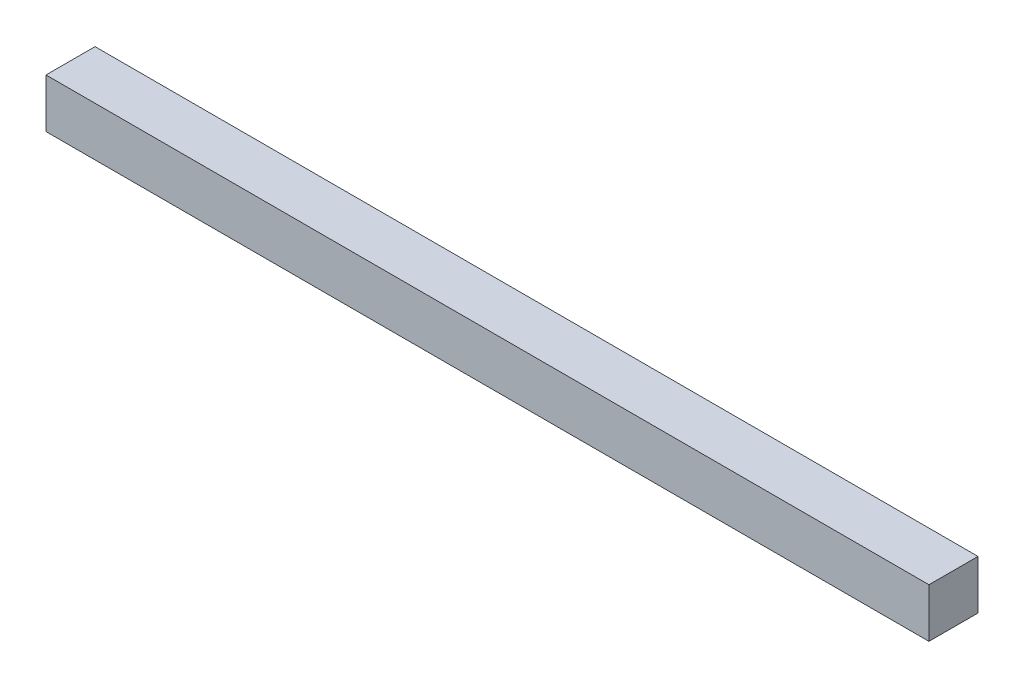
SolidWorks part; units mm, degrees
ref_plane "Front Plane" through (0, 0, 0) normal (0, 0, 1) x (1, 0, 0)
ref_plane "Top Plane" through (0, 0, 0) normal (0, 1, 0) x (1, 0, 0)
ref_plane "Right Plane" through (0, 0, 0) normal (1, 0, 0) x (0, 0, -1)
sketch "Sketch1" plane through (0, 0, 0) normal (1, 0, 0) x (0, 0, -1)
  line L1 (-19.05, 19.05) -> (19.05, 19.05)
  line L2 (-19.05, 19.05) -> (-19.05, -19.05)
  line L3 (-19.05, -19.05) -> (19.05, -19.05)
  line L4 (19.05, 19.05) -> (19.05, -19.05)
  line L5 (-19.05, 19.05) -> (19.05, -19.05) construction
  line L6 (-19.05, -19.05) -> (19.05, 19.05) construction
  point P0 (0, 0)
  dimension "D1" = 38.1
  dimension "D2" = 38.1
extrude "Boss-Extrude1" add sketch "Sketch1" along normal blind 685.8
